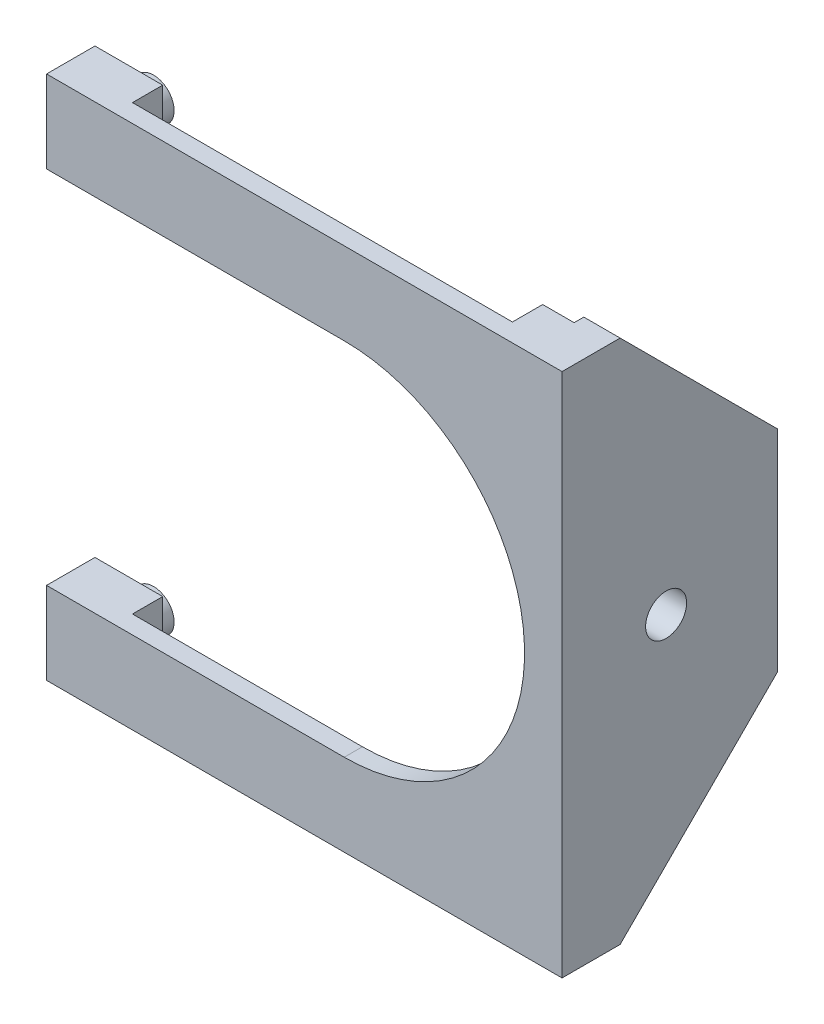
SolidWorks part; units mm, degrees
material "6061-T6 Al"
ref_plane "Front" through (0, 0, 0) normal (0, 0, 1) x (1, 0, 0)
ref_plane "Top" through (0, 0, 0) normal (0, 1, 0) x (1, 0, 0)
ref_plane "Right" through (0, 0, 0) normal (1, 0, 0) x (0, 0, -1)
sketch "Sketch1 w/mock PCB" plane through (0, 0, 0) normal (0, 0, 1) x (1, 0, 0)
  line L0 (0, 27.559) -> (0, -27.559) construction
  line L1 (-19.05, 18.923) -> (-50.292, 18.923)
  line L2 (-50.292, 27.559) -> (3.81, 27.559)
  line L3 (-50.292, 27.559) -> (-50.292, 18.923)
  line L4 (-50.292, -27.559) -> (3.81, -27.559)
  line L6 (3.81, 27.559) -> (3.81, -27.559)
  line L7 (-19.05, -18.923) -> (-50.292, -18.923)
  line L8 (-50.292, -18.923) -> (-50.292, -27.559)
  arc A0 (-19.05, -18.923) -> (-19.05, 18.923) centre (-19.05, 0) ccw
  point P5 (-25.908, 20.828)
  point P6 (25.908, 20.828)
  point P7 (25.908, -20.828)
  point P8 (-25.908, -20.828)
  point P22 (0, 29.1773)
  point P63 (-25.781, -19.05)
  point P64 (25.781, -19.05)
  dimension "D5" = 19.05
  dimension "D4" = 37.846
  dimension "D1" = 50.292
  dimension "D2" = 55.118
  dimension "D3" = 3.81
extrude "Boss-Extrude1" add sketch "Sketch1 w/mock PCB" against normal blind 22.606
sketch "Sketch1" plane through (0, -27.559, 0) normal (0, -1, 0) x (1, 0, 0)
  line L3 (-3.302, -5.08) -> (-3.302, -1.905)
  line L4 (3.81, 0) -> (-50.292, 0)
  line L5 (3.81, -22.606) -> (3.81, 0)
  line L6 (-50.292, -22.606) -> (3.81, -22.606)
  line L7 (-50.292, 0) -> (-50.292, -22.606)
  line L8 (-50.292, -22.606) -> (3.81, -22.606) construction
  line L9 (0, -5.08) -> (0, -22.606)
  line L10 (0, -5.08) -> (-3.302, -5.08)
  line L11 (-50.292, -22.606) -> (-50.292, -5.08)
  line L12 (-3.302, -1.905) -> (-43.18, -1.905)
  line L19 (-50.292, -22.606) -> (0, -22.606)
  line L20 (-50.292, 0) -> (3.81, 0) construction
  line L21 (-43.18, -1.905) -> (-43.18, -5.08)
  line L22 (-43.18, -5.08) -> (-50.292, -5.08)
  point P15 (1.7113, 0)
  dimension "D2" = 1.905
  dimension "D3" = 5.08
  dimension "D4" = 3.302
  dimension "D5" = 7.112
  dimension "D1" = 0
extrude "Cut-Extrude1" cut sketch "Sketch1" against normal through all
hole_wizard "#8 Clearance Hole1" positions "Sketch3" profile "Sketch2" hole size "#8" standard "ANSI Inch" end condition up to next
sketch "Sketch3" plane through (3.81, 0, 0) normal (1, 0, 0) x (0, 0, -1)
  line L0 (5.08, 27.559) -> (5.08, -27.559) construction
  point P0 (10.922, 0)
  dimension "D1" = 5.842
sketch "Sketch2" plane through (3.81, 0, -10.922) normal (0, 1, 0) x (0, 0, -1)
  line L0 (0, 0) -> (0, 3.81)
  line L1 (0, 3.81) -> (2.1526, 3.81)
  line L2 (2.1526, 3.81) -> (2.1526, 0)
  line L5 (2.1526, 0) -> (0, 0)
  line L11 (0, -6.35) -> (0, 107.95) construction
  dimension "Thru Hole Dia." = 4.3053
  dimension "Thru Hole Depth" = 3.81
ref_plane "Boss Plane" through (0, 23.241, 0) normal (0, 1, 0) x (1, 0, 0)
sketch "Sketch8" plane through (0, 23.241, 0) normal (0, 1, 0) x (1, 0, 0)
  line L0 (-43.18, 5.08) -> (-50.292, 5.08) construction
  line L1 (-46.736, 5.08) -> (-46.736, 2.921) construction
  line L2 (-46.736, 8.0518) -> (-46.736, 5.08)
  line L3 (-46.736, 5.08) -> (-44.577, 5.08)
  line L4 (-44.577, 7.6735) -> (-44.577, 5.08)
  line L6 (0, 22.606) -> (0, 5.08) construction
  line L7 (-46.736, 1.7018) -> (-44.577, 7.6735) construction
  arc A0 (-46.736, 8.0518) -> (-44.577, 7.6735) centre (-46.736, 1.7018) cw
  point P12 (-49.1142, 5.08)
  dimension "D4" = 6.35
  dimension "D1" = 46.736
  dimension "D2" = 2.9718
  dimension "D3" = 4.318
  dimension "D5" = 19.877
revolve "Revolve1" add sketch "Sketch8" angle 360 about L1
mirror "Mirror1" about plane through (0, 0, 0) normal (0, 1, 0) of "Revolve1"
chamfer "Chamfer1" distance 16.51 angle 45 2 edges at (1.905, -27.559, -22.606) (1.905, 27.559, -22.606)
